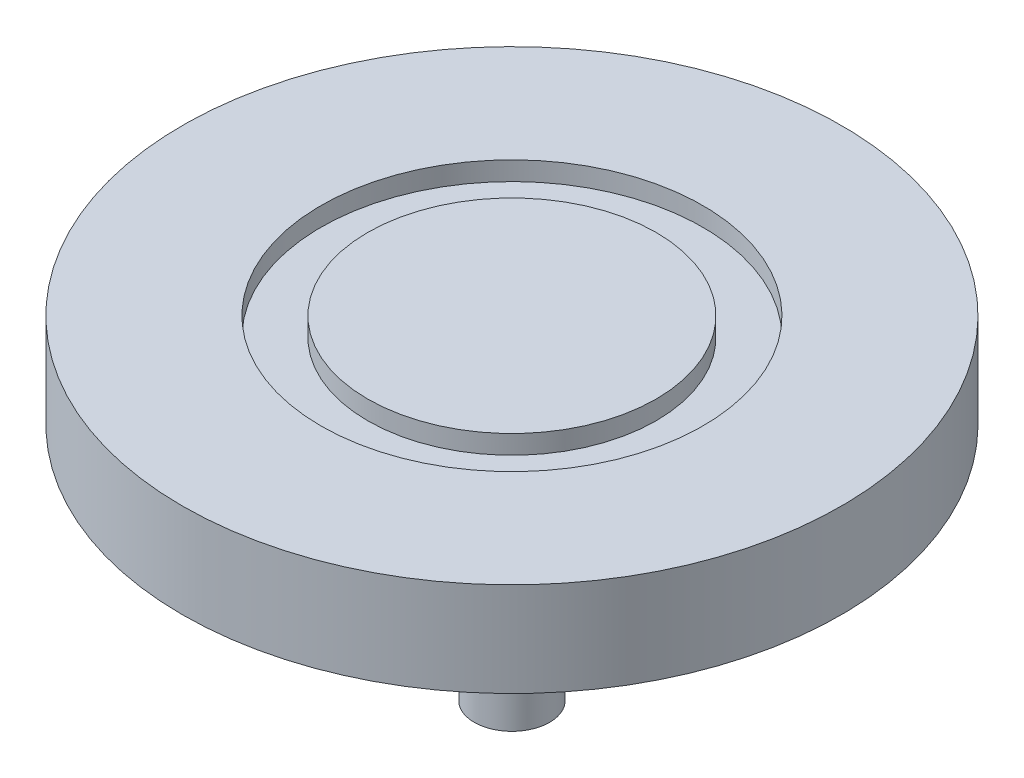
SolidWorks part; units mm, degrees
ref_plane "Front Plane" through (0, 0, 0) normal (0, 0, 1) x (1, 0, 0)
ref_plane "Top Plane" through (0, 0, 0) normal (0, 1, 0) x (1, 0, 0)
ref_plane "Right Plane" through (0, 0, 0) normal (1, 0, 0) x (0, 0, -1)
sketch "Sketch1" plane through (0, 0, 0) normal (0, 1, 0) x (1, 0, 0)
  circle A0 centre (0, 0) radius 35
  dimension "D1" = 70
extrude "Boss-Extrude1" add sketch "Sketch1" along normal blind 10
sketch "Sketch2" plane through (0, 10, 0) normal (0, 1, 0) x (1, 0, 0)
  circle A0 centre (0, 0) radius 20.2802
  circle A1 centre (0, 0) radius 15.3212
  point P5 (0.1626, 0)
extrude "Cut-Extrude1" cut sketch "Sketch2" against normal blind 2
sketch "Sketch3" plane through (0, 0, 0) normal (0, -1, 0) x (1, 0, 0)
  circle A0 centre (0, 0) radius 4
  dimension "D1" = 8
extrude "Boss-Extrude2" add sketch "Sketch3" along normal blind 25.4
